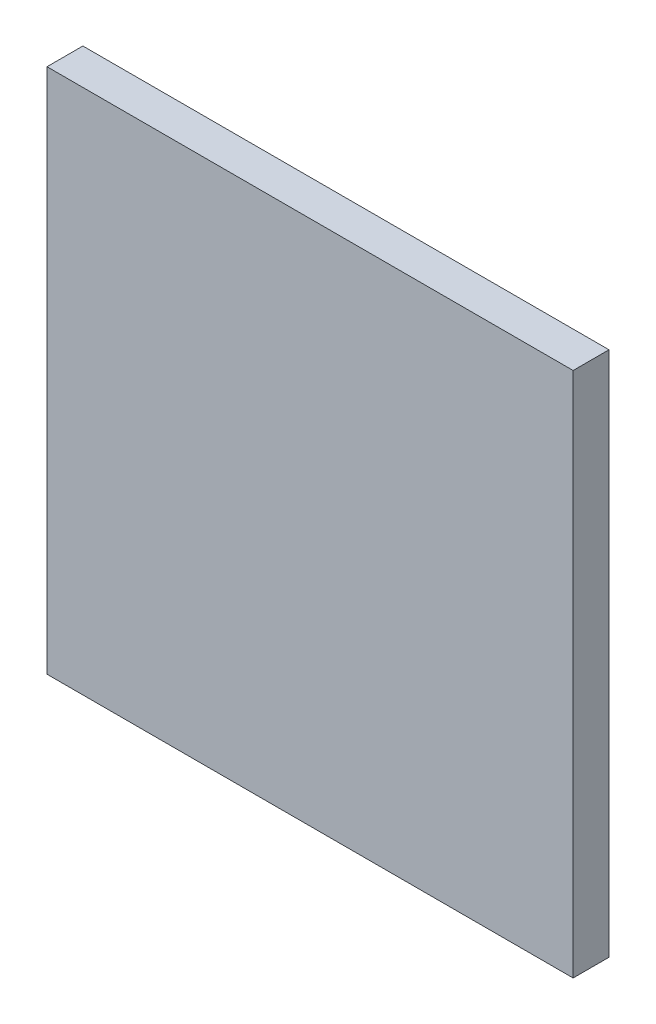
SolidWorks part; units mm, degrees
ref_plane "Front Plane" through (0, 0, 0) normal (0, 0, 1) x (1, 0, 0)
ref_plane "Top Plane" through (0, 0, 0) normal (0, 1, 0) x (1, 0, 0)
ref_plane "Right Plane" through (0, 0, 0) normal (1, 0, 0) x (0, 0, -1)
sketch "Sketch1" plane through (0, 0, 0) normal (0, 0, 1) x (1, 0, 0)
  line L1 (0, 279.4) -> (279.4, 279.4)
  line L2 (0, 279.4) -> (0, 0)
  line L3 (0, 0) -> (279.4, 0)
  line L4 (279.4, 279.4) -> (279.4, 0)
extrude "Boss-Extrude1" add sketch "Sketch1" along normal blind 19.05
sketch "Sketch4" plane through (0, 0, 0) normal (0, 0, -1) x (-1, 0, 0)
  circle A0 centre (-9.525, 9.525) radius 3.175
extrude "Cut-Extrude8" cut sketch "Sketch4" against normal blind 12.7
pattern_linear "LPattern1" count 6 spacing 50.8 along (0, 1, 0) count 6 spacing 50.8 along (1, 0, 0) of "Cut-Extrude8"
